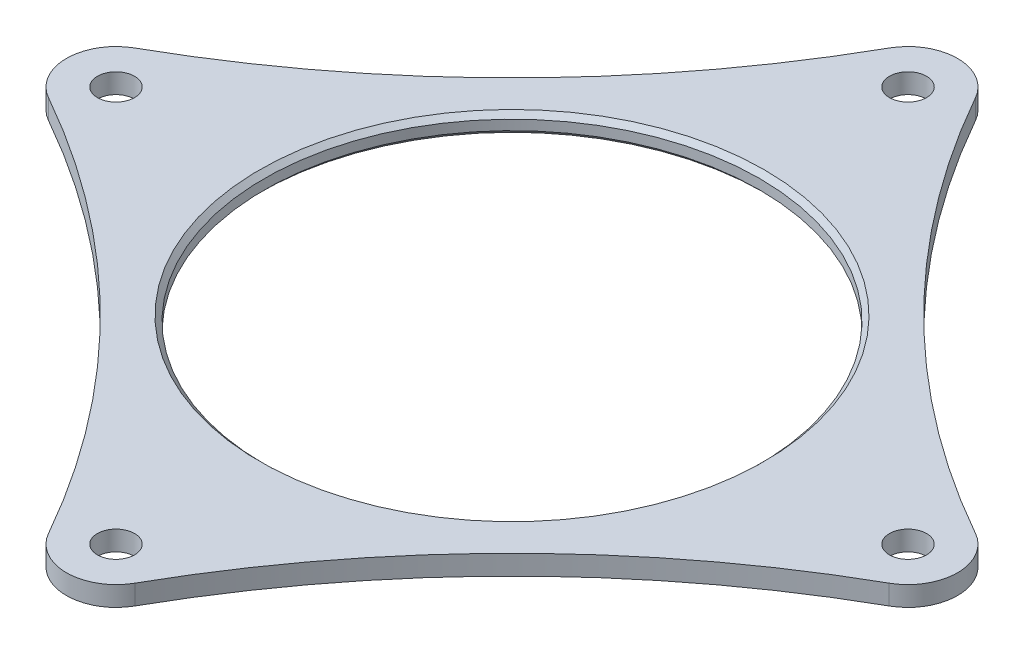
SolidWorks part; units mm, degrees
ref_plane "Front Plane" through (0, 0, 0) normal (0, 0, 1) x (1, 0, 0)
ref_plane "Top Plane" through (0, 0, 0) normal (0, 1, 0) x (1, 0, 0)
ref_plane "Right Plane" through (0, 0, 0) normal (1, 0, 0) x (0, 0, -1)
sketch "Sketch1" plane through (0, 0, 0) normal (0, 1, 0) x (1, 0, 0)
  line L1 (-114.3, -114.3) -> (114.3, -114.3)
  line L2 (-114.3, -114.3) -> (-114.3, 114.3)
  line L3 (-114.3, 114.3) -> (114.3, 114.3)
  line L4 (114.3, -114.3) -> (114.3, 114.3)
  line L5 (-114.3, -114.3) -> (114.3, 114.3) construction
  line L6 (-114.3, 114.3) -> (114.3, -114.3) construction
  point P0 (0, 0)
  dimension "D1" = 228.6
extrude "Boss-Extrude1" add sketch "Sketch1" along normal blind 5.08
sketch "Sketch2" plane through (0, 5.08, 0) normal (0, 1, 0) x (1, 0, 0)
  circle A0 centre (0, 0) radius 63.5
  circle A1 centre (0, 0) radius 101.6 construction
  dimension "D2" = 127
  dimension "D3" = 203.2
extrude "Cut-Extrude1" cut sketch "Sketch2" against normal through all
sketch "Sketch3" plane through (0, 5.08, 0) normal (0, 1, 0) x (1, 0, 0)
  line L0 (0, 101.6) -> (0, 0) construction
  line L1 (0, 0) -> (101.6, 0) construction
  line L4 (114.3, 114.3) -> (-114.3, 114.3) construction
  line L5 (114.3, -114.3) -> (114.3, 114.3) construction
  line L6 (114.3, 114.3) -> (0, 114.3)
  line L7 (114.3, 0) -> (114.3, 114.3)
  circle A0 centre (101.6, 0) radius 4.7625 construction
  circle A1 centre (0, 101.6) radius 4.7625 construction
  arc A2 (11.0674, 107.8293) -> (0, 114.3) centre (0, 101.6) ccw
  arc A3 (114.3, 0) -> (107.8293, 11.0674) centre (101.6, 0) ccw
  arc A4 (11.0674, 107.8293) -> (107.8293, 11.0674) centre (232.4144, 232.4144) ccw
  dimension "D2" = 9.525
  dimension "D3" = 25.4
  dimension "D4" = 254
  dimension "D1" = 101.6
extrude "Cut-Extrude2" cut sketch "Sketch3" against normal through all
pattern_circular "CirPattern1" count 4 over 360 about axis through (0, 0, 0) along (0, 1, 0) of "Cut-Extrude2"
hole_wizard "3/8 (0.375) Diameter Hole1" positions "Sketch6" profile "Sketch7" hole size "3/8" standard "ANSI Inch" end condition up to next
sketch "Sketch6" plane through (0, 5.08, 0) normal (0, 1, 0) x (1, 0, 0)
  arc A3 (107.8293, -11.0674) -> (107.8293, 11.0674) centre (101.6, 0) ccw construction
  arc A4 (107.8293, -11.0674) -> (107.8293, 11.0674) centre (101.6, 0) ccw
  point P0 (101.6, 0)
sketch "Sketch7" plane through (101.6, 5.08, 0) normal (1, 0, 0) x (0, 0, 1)
  line L0 (0, 0) -> (0, 5.081)
  line L1 (0, 5.081) -> (4.7625, 5.081)
  line L2 (4.7625, 5.081) -> (4.7625, 0)
  line L5 (4.7625, 0) -> (0, 0)
  line L11 (0, -6.35) -> (0, 107.95) construction
  dimension "Thru Hole Dia." = 9.525
  dimension "Thru Hole Depth" = 5.081
pattern_circular "CirPattern2" count 4 over 360 about axis through (0, 0, 0) along (0, 1, 0) of "3/8 (0.375) Diameter Hole1"
chamfer "Chamfer1" distance 1.27 angle 45 2 edges at (0, 5.08, 63.5) (0, 0, 63.5)
